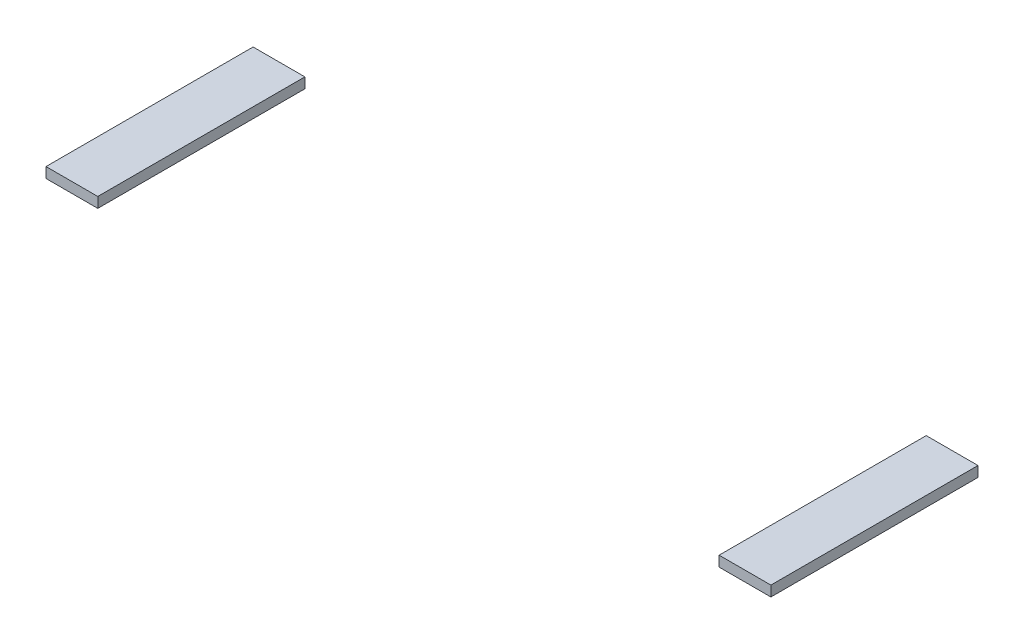
SolidWorks part; units mm, degrees
ref_plane "Front Plane" through (0, 0, 0) normal (0, 0, 1) x (1, 0, 0)
ref_plane "Top Plane" through (0, 0, 0) normal (0, 1, 0) x (1, 0, 0)
ref_plane "Right Plane" through (0, 0, 0) normal (1, 0, 0) x (0, 0, -1)
sketch "Sketch1" plane through (0, 0, 0) normal (0, 0, 1) x (1, 0, 0)
  line L1 (0, 0) -> (2, 0)
  line L2 (0, 0) -> (0, 0.4)
  line L3 (0, 0.4) -> (2, 0.4)
  line L4 (2, 0) -> (2, 0.4)
  line L5 (26, 0.4) -> (28, 0.4)
  line L6 (26, 0.4) -> (26, 0)
  line L7 (26, 0) -> (28, 0)
  line L8 (28, 0.4) -> (28, 0)
  point P9 (28, 0.2)
  dimension "D1" = 0.4
  dimension "D2" = 2
  dimension "D3" = 2
  dimension "D4" = 0.4
  dimension "D5" = 28
extrude "Boss-Extrude1" add sketch "Sketch1" along normal blind 8
